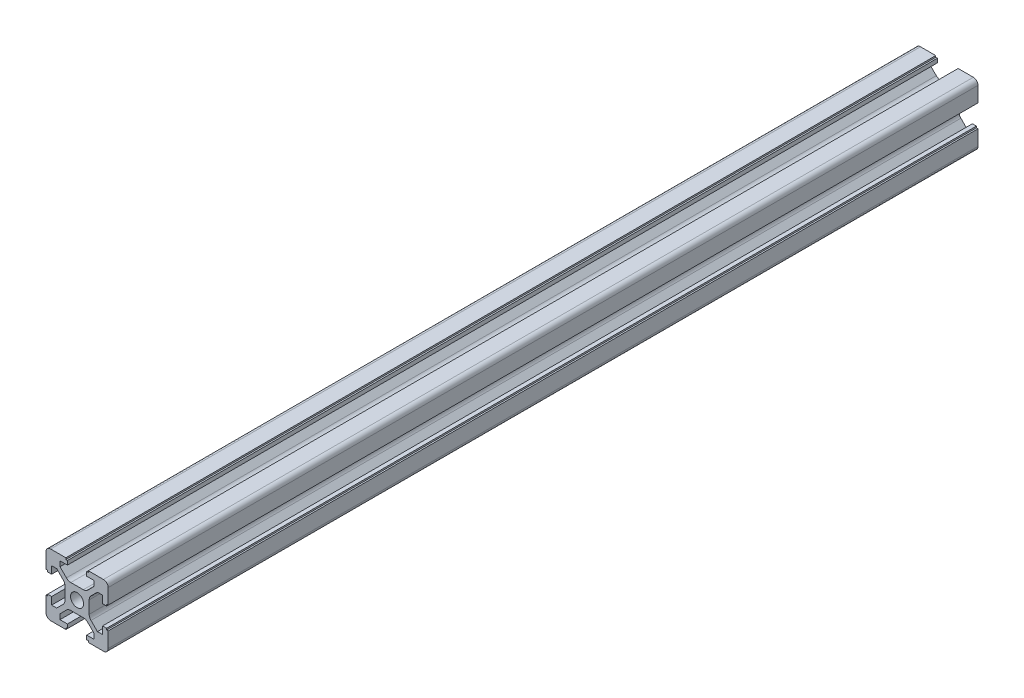
SolidWorks part; units mm, degrees
material "6061 合金"
ref_plane "前视基准面" through (0, 0, 0) normal (0, 0, 1) x (1, 0, 0)
ref_plane "上视基准面" through (0, 0, 0) normal (0, 1, 0) x (1, 0, 0)
ref_plane "右视基准面" through (0, 0, 0) normal (1, 0, 0) x (0, 0, -1)
sketch "草图1" plane through (0, 0, 0) normal (0, 0, 1) x (1, 0, 0)
  line L0 (-3.4251, 4.4858) -> (-5.5, 6.5607)
  line L6 (-5.5, 6.5607) -> (-5.5, 8.2)
  line L7 (-5.5, 8.2) -> (-3.1, 8.2)
  line L22 (-3.1, 8.2) -> (-3.1, 9.5)
  line L41 (-3.6, 10) -> (-8.5, 10)
  line L42 (0, 0) -> (-29.7212, 29.7212) construction
  line L43 (0, -8.5755) -> (0, 20.7623) construction
  line L44 (-10, 3.6) -> (-10, 8.5)
  line L46 (-8.2, 5.5) -> (-8.2, 3.1)
  line L47 (-6.5607, 5.5) -> (-8.2, 5.5)
  line L48 (-4.4858, 3.4251) -> (-6.5607, 5.5)
  line L49 (4.4858, 3.4251) -> (6.5607, 5.5)
  line L50 (6.5607, 5.5) -> (8.2, 5.5)
  line L51 (8.2, 5.5) -> (8.2, 3.1)
  line L53 (10, 3.6) -> (10, 8.5)
  line L54 (3.6, 10) -> (8.5, 10)
  line L56 (5.5, 8.2) -> (3.1, 8.2)
  line L57 (5.5, 6.5607) -> (5.5, 8.2)
  line L58 (3.4251, 4.4858) -> (5.5, 6.5607)
  line L59 (11, 0) -> (-11, 0) construction
  line L60 (3.4251, -4.4858) -> (5.5, -6.5607)
  line L61 (5.5, -6.5607) -> (5.5, -8.2)
  line L62 (5.5, -8.2) -> (3.1, -8.2)
  line L64 (3.6, -10) -> (8.5, -10)
  line L65 (10, -3.6) -> (10, -8.5)
  line L67 (8.2, -5.5) -> (8.2, -3.1)
  line L68 (6.5607, -5.5) -> (8.2, -5.5)
  line L69 (4.4858, -3.4251) -> (6.5607, -5.5)
  line L70 (-4.4858, -3.4251) -> (-6.5607, -5.5)
  line L71 (-6.5607, -5.5) -> (-8.2, -5.5)
  line L72 (-8.2, -5.5) -> (-8.2, -3.1)
  line L74 (-10, -3.6) -> (-10, -8.5)
  line L75 (-3.6, -10) -> (-8.5, -10)
  line L77 (-5.5, -8.2) -> (-3.1, -8.2)
  line L78 (-5.5, -6.5607) -> (-5.5, -8.2)
  line L79 (-3.4251, -4.4858) -> (-5.5, -6.5607)
  line L80 (-3.9, -2.0109) -> (-3.9, 2.0109)
  line L81 (-2.0109, 3.9) -> (2.0109, 3.9)
  line L82 (3.9, 2.0109) -> (3.9, -2.0109)
  line L83 (2.0109, -3.9) -> (-2.0109, -3.9)
  line L84 (-3.1, 9.5) -> (-3.6, 9.5)
  line L85 (-3.6, 9.5) -> (-3.6, 10)
  line L86 (3.6, 9.5) -> (3.6, 10)
  line L87 (3.1, 9.5) -> (3.6, 9.5)
  line L88 (3.1, 8.2) -> (3.1, 9.5)
  line L89 (-9.5, 3.1) -> (-9.5, 3.6)
  line L90 (-9.5, 3.6) -> (-10, 3.6)
  line L91 (-8.2, 3.1) -> (-9.5, 3.1)
  line L92 (8.2, 3.1) -> (9.5, 3.1)
  line L93 (9.5, 3.6) -> (10, 3.6)
  line L94 (9.5, 3.1) -> (9.5, 3.6)
  line L95 (9.5, -3.1) -> (9.5, -3.6)
  line L96 (9.5, -3.6) -> (10, -3.6)
  line L97 (8.2, -3.1) -> (9.5, -3.1)
  line L98 (3.1, -8.2) -> (3.1, -9.5)
  line L99 (3.1, -9.5) -> (3.6, -9.5)
  line L100 (3.6, -9.5) -> (3.6, -10)
  line L101 (-3.6, -9.5) -> (-3.6, -10)
  line L102 (-3.1, -9.5) -> (-3.6, -9.5)
  line L103 (-3.1, -8.2) -> (-3.1, -9.5)
  line L104 (-8.2, -3.1) -> (-9.5, -3.1)
  line L105 (-9.5, -3.6) -> (-10, -3.6)
  line L106 (-9.5, -3.1) -> (-9.5, -3.6)
  circle A0 centre (0, 0) radius 2.1
  arc A1 (-10, -8.5) -> (-8.5, -10) centre (-8.5, -8.5) ccw
  arc A2 (8.5, -10) -> (10, -8.5) centre (8.5, -8.5) ccw
  arc A3 (10, 8.5) -> (8.5, 10) centre (8.5, 8.5) ccw
  arc A4 (-8.5, 10) -> (-10, 8.5) centre (-8.5, 8.5) ccw
  arc A5 (-4.4858, 3.4251) -> (-3.9, 2.0109) centre (-5.9, 2.0109) cw
  arc A6 (-3.4251, 4.4858) -> (-2.0109, 3.9) centre (-2.0109, 5.9) ccw
  arc A7 (3.4251, 4.4858) -> (2.0109, 3.9) centre (2.0109, 5.9) cw
  arc A8 (4.4858, 3.4251) -> (3.9, 2.0109) centre (5.9, 2.0109) ccw
  arc A9 (4.4858, -3.4251) -> (3.9, -2.0109) centre (5.9, -2.0109) cw
  arc A10 (-4.4858, -3.4251) -> (-3.9, -2.0109) centre (-5.9, -2.0109) ccw
  arc A11 (3.4251, -4.4858) -> (2.0109, -3.9) centre (2.0109, -5.9) ccw
  arc A12 (-3.4251, -4.4858) -> (-2.0109, -3.9) centre (-2.0109, -5.9) cw
  point P74 (-10, -10)
  point P77 (10, -10)
  point P80 (10, 10)
  point P83 (-10, 10)
  point P86 (-3.9, 2.8393)
  point P89 (-2.8393, 3.9)
  point P92 (2.8393, 3.9)
  point P95 (3.9, 2.8393)
  point P98 (3.9, -2.8393)
  point P101 (-3.9, -2.8393)
  point P104 (2.8393, -3.9)
  point P107 (-2.8393, -3.9)
  dimension "D8" = 4.2
  dimension "D7" = 1.5
  dimension "D12" = 2
  dimension "D1" = 45
  dimension "D2" = 20
  dimension "D3" = 0.5
  dimension "D4" = 6.2
  dimension "D5" = 11
  dimension "D6" = 1.5
  dimension "D9" = 0.5
  dimension "D10" = 1.8
  dimension "D11" = 6.1
extrude "凸台-拉伸1" add sketch "草图1" along normal mid plane 280
